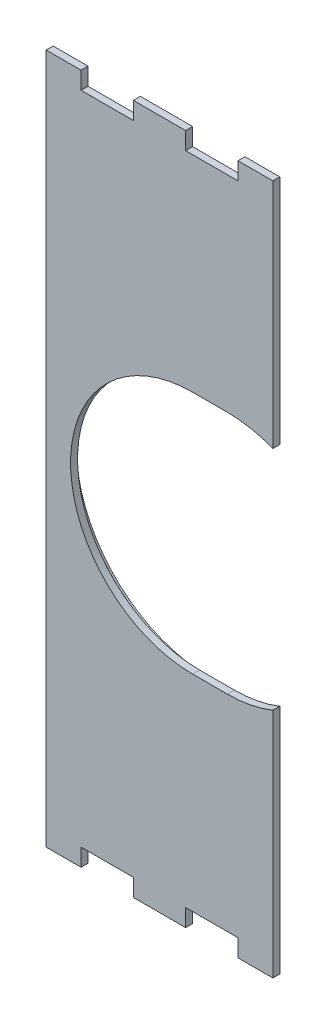
SolidWorks part; units mm, degrees
ref_plane "Front Plane" through (0, 0, 0) normal (0, 0, 1) x (1, 0, 0)
ref_plane "Top Plane" through (0, 0, 0) normal (0, 1, 0) x (1, 0, 0)
ref_plane "Right Plane" through (0, 0, 0) normal (1, 0, 0) x (0, 0, -1)
sketch "Sketch1" plane through (0, 0, 0) normal (0, 0, 1) x (1, 0, 0)
  line L1 (-374.65, -246.38) -> (-292.1, -246.38)
  line L2 (-374.65, -246.38) -> (-374.65, 5.08)
  line L3 (-374.65, 5.08) -> (-292.1, 5.08)
  line L4 (-292.1, -246.38) -> (-292.1, 5.08)
extrude "Boss-Extrude1" add sketch "Sketch1" along normal blind 6.35
sketch "Sketch3" plane through (0, 0, 6.35) normal (0, 0, 1) x (1, 0, 0)
  line L0 (-374.65, -120.65) -> (-351.9735, -120.65) construction
  line L1 (-374.65, 5.08) -> (-374.65, -246.38) construction
sketch "Sketch2" plane through (0, 5.08, 0) normal (0, 1, 0) x (1, 0, 0)
  line L0 (-304.8, 0) -> (-323.85, 0)
  line L1 (-342.9, 0) -> (-361.95, 0)
  line L2 (-374.65, -6.35) -> (-292.1, -6.35)
  line L46 (0, 33.02) -> (-6.35, 33.02)
  line L47 (-6.35, 33.02) -> (-6.35, 50.8)
  line L48 (-6.35, 50.8) -> (0, 50.8)
  line L49 (0, 50.8) -> (0, 69.85)
  line L50 (0, 69.85) -> (-381, 69.85)
  line L51 (-381, 69.85) -> (-381, 57.15)
  line L52 (-381, 57.15) -> (-374.65, 57.15)
  line L53 (-374.65, 57.15) -> (-374.65, 44.45)
  line L54 (-374.65, 44.45) -> (-381, 44.45)
  line L55 (-381, 44.45) -> (-381, 25.4)
  line L56 (-381, 25.4) -> (-374.65, 25.4)
  line L57 (-374.65, 25.4) -> (-374.65, 12.7)
  line L58 (-374.65, 12.7) -> (-381, 12.7)
  line L59 (-381, 12.7) -> (-381, 0)
  line L60 (-374.65, -6.35) -> (-374.65, 0)
  line L61 (-374.65, 0) -> (-361.95, 0)
  line L62 (-361.95, 0) -> (-361.95, -6.35)
  line L63 (-361.95, -6.35) -> (-342.9, -6.35)
  line L64 (-342.9, -6.35) -> (-342.9, 0)
  line L65 (-342.9, 0) -> (-323.85, 0)
  line L66 (-323.85, 0) -> (-323.85, -6.35)
  line L67 (-323.85, -6.35) -> (-304.8, -6.35)
  line L68 (-304.8, -6.35) -> (-304.8, 0)
  line L69 (-304.8, 0) -> (-292.1, 0)
  line L70 (-292.1, 0) -> (-292.1, -6.35)
  line L71 (-292.1, -6.35) -> (-285.75, -6.35)
  line L72 (-285.75, -6.35) -> (-285.75, 44.45)
  line L73 (-279.4, 50.8) -> (-215.9, 50.8)
  line L74 (-209.55, 44.45) -> (-209.55, -57.15)
  line L75 (-215.9, -63.5) -> (-215.9, -69.85)
  line L76 (-215.9, -69.85) -> (-196.85, -69.85)
  line L77 (-196.85, -69.85) -> (-196.85, -63.5)
  line L78 (-203.2, -57.15) -> (-203.2, 44.45)
  line L79 (-196.85, 50.8) -> (-131.8807, 50.8)
  line L80 (-125.7444, 46.0836) -> (-113.8144, 1.27)
  line L81 (-97.0614, 1.27) -> (-6.35, 1.27)
  line L82 (-97.0614, 1.27) -> (-6.35, 1.27)
  line L83 (-113.8144, 1.27) -> (-107.597, 1.27)
  line L84 (-113.8144, 1.27) -> (-107.597, 1.27)
  line L89 (-6.35, 1.27) -> (-6.35, 13.97)
  line L90 (-6.35, 13.97) -> (0, 13.97)
  line L91 (0, 13.97) -> (0, 33.02)
  line L106 (-374.65, -6.35) -> (-374.65, 0)
  line L107 (-374.65, 0) -> (-361.95, 0)
  line L108 (-361.95, 0) -> (-361.95, -6.35)
  line L109 (-361.95, -6.35) -> (-342.9, -6.35)
  line L110 (-342.9, -6.35) -> (-342.9, 0)
  line L111 (-342.9, 0) -> (-323.85, 0)
  line L112 (-323.85, 0) -> (-323.85, -6.35)
  line L113 (-323.85, -6.35) -> (-304.8, -6.35)
  line L114 (-304.8, -6.35) -> (-304.8, 0)
  line L115 (-304.8, 0) -> (-292.1, 0)
  line L116 (-292.1, 0) -> (-292.1, -6.35)
  arc A7 (-381, 0) -> (-374.65, -6.35) centre (-374.65, 0) ccw
  arc A8 (-279.4, 50.8) -> (-285.75, 44.45) centre (-279.4, 44.45) ccw
  arc A9 (-209.55, 44.45) -> (-215.9, 50.8) centre (-215.9, 44.45) ccw
  arc A10 (-215.9, -63.5) -> (-209.55, -57.15) centre (-215.9, -57.15) ccw
  arc A11 (-203.2, -57.15) -> (-196.85, -63.5) centre (-196.85, -57.15) ccw
  arc A12 (-196.85, 50.8) -> (-203.2, 44.45) centre (-196.85, 44.45) ccw
  arc A13 (-125.7444, 46.0836) -> (-131.8807, 50.8) centre (-131.8807, 44.45) ccw
  ellipse E2 centre (-102.3292, 8.5961) end of major axis (-102.3292, -2.0421) minor radius 7.2651 (-97.0614, 1.27) -> (-107.597, 1.27) ccw
  ellipse E3 centre (-102.3292, 8.5961) end of major axis (-102.3292, -2.0421) minor radius 7.2651 (-97.0614, 1.27) -> (-107.597, 1.27) ccw
  line M55 (-292.1, 0) -> (-374.65, 0)
  dimension "D1" = 0
extrude "Cut-Extrude2" cut sketch "Sketch2" against normal blind 6.35 contours L2 L110 L108 M55 | L2 L114 L112 M55
sketch "Sketch5" plane through (0, -246.38, 0) normal (0, -1, 0) x (1, 0, 0)
  line L0 (-374.65, 6.35) -> (-351.9735, 6.35) construction
  line L1 (-361.95, 6.35) -> (-342.9, 6.35)
  line L2 (-361.95, 6.35) -> (-361.95, 0)
  line L3 (-361.95, 0) -> (-342.9, 0)
  line L4 (-342.9, 6.35) -> (-342.9, 0)
  line L5 (-374.65, 0) -> (-292.1, 0) construction
  line L6 (-374.65, 6.35) -> (-292.1, 6.35) construction
  line L7 (-323.85, 6.35) -> (-304.8, 6.35)
  line L8 (-323.85, 6.35) -> (-323.85, 0)
  line L9 (-323.85, 0) -> (-304.8, 0)
  line L10 (-304.8, 6.35) -> (-304.8, 0)
  line L11 (-374.65, 6.35) -> (-374.65, 0) construction
  line L12 (-342.9, 6.35) -> (-342.9, 0) construction
  line M5 (-374.65, 0) -> (-292.1, 0)
  line M7 (-292.1, 6.35) -> (-374.65, 6.35)
  dimension "D1" = 12.7
  dimension "D2" = 19.05
  dimension "D3" = 19.05
  dimension "D4" = 19.05
extrude "Cut-Extrude4" cut sketch "Sketch5" against normal blind 6.35 contours L4 L2 M7 M5 | L10 L8 M7 M5
sketch "Sketch6" plane through (0, 0, 6.35) normal (0, 0, 1) x (1, 0, 0)
  line L0 (-321.31, -165.1) -> (-308.61, -165.1)
  line L1 (-321.31, -76.2) -> (-308.61, -76.2)
  line L2 (-374.65, 5.08) -> (-374.65, -246.38) construction
  arc A0 (-321.31, -76.2) -> (-321.31, -165.1) centre (-321.31, -120.65) ccw
  arc A1 (-308.61, -165.1) -> (-308.61, -76.2) centre (-308.61, -120.65) ccw
  dimension "D1" = 88.9
  dimension "D2" = 88.9
  dimension "D3" = 12.7
  dimension "D4" = 53.34
extrude "Cut-Extrude5" cut sketch "Sketch6" against normal through all
sketch "Sketch8" plane through (0, 0, 0) normal (0, 0, -1) x (-1, 0, 0)
  line L46 (308.61, -74.422) -> (321.31, -74.422)
  line L47 (321.31, -166.878) -> (308.61, -166.878)
  line L48 (293.878, -164.4678) -> (293.878, -244.602)
  line L49 (293.878, -244.602) -> (303.022, -244.602)
  line L50 (303.022, -244.602) -> (303.022, -238.252)
  line L51 (303.022, -238.252) -> (325.628, -238.252)
  line L52 (325.628, -238.252) -> (325.628, -244.602)
  line L53 (325.628, -244.602) -> (341.122, -244.602)
  line L54 (341.122, -244.602) -> (341.122, -238.252)
  line L55 (341.122, -238.252) -> (363.728, -238.252)
  line L56 (363.728, -238.252) -> (363.728, -244.602)
  line L57 (363.728, -244.602) -> (372.872, -244.602)
  line L58 (372.872, -244.602) -> (372.872, 3.302)
  line L59 (372.872, 3.302) -> (363.728, 3.302)
  line L60 (363.728, 3.302) -> (363.728, -3.048)
  line L61 (363.728, -3.048) -> (341.122, -3.048)
  line L62 (341.122, -3.048) -> (341.122, 3.302)
  line L63 (341.122, 3.302) -> (325.628, 3.302)
  line L64 (325.628, 3.302) -> (325.628, -3.048)
  line L65 (325.628, -3.048) -> (303.022, -3.048)
  line L66 (303.022, -3.048) -> (303.022, 3.302)
  line L67 (303.022, 3.302) -> (293.878, 3.302)
  line L68 (293.878, 3.302) -> (293.878, -76.8322)
  line L69 (308.61, -74.422) -> (321.31, -74.422)
  line L70 (321.31, -166.878) -> (308.61, -166.878)
  line L71 (293.878, -164.4678) -> (293.878, -244.602)
  line L72 (293.878, -244.602) -> (303.022, -244.602)
  line L73 (303.022, -244.602) -> (303.022, -238.252)
  line L74 (303.022, -238.252) -> (325.628, -238.252)
  line L75 (325.628, -238.252) -> (325.628, -244.602)
  line L76 (325.628, -244.602) -> (341.122, -244.602)
  line L77 (341.122, -244.602) -> (341.122, -238.252)
  line L78 (341.122, -238.252) -> (363.728, -238.252)
  line L79 (363.728, -238.252) -> (363.728, -244.602)
  line L80 (363.728, -244.602) -> (372.872, -244.602)
  line L81 (372.872, -244.602) -> (372.872, 3.302)
  line L82 (372.872, 3.302) -> (363.728, 3.302)
  line L83 (363.728, 3.302) -> (363.728, -3.048)
  line L84 (363.728, -3.048) -> (341.122, -3.048)
  line L85 (341.122, -3.048) -> (341.122, 3.302)
  line L86 (341.122, 3.302) -> (325.628, 3.302)
  line L87 (325.628, 3.302) -> (325.628, -3.048)
  line L88 (325.628, -3.048) -> (303.022, -3.048)
  line L89 (303.022, -3.048) -> (303.022, 3.302)
  line L90 (303.022, 3.302) -> (293.878, 3.302)
  line L91 (293.878, 3.302) -> (293.878, -76.8322)
  arc A6 (308.61, -74.422) -> (293.878, -76.8322) centre (308.61, -120.65) ccw
  arc A7 (321.31, -166.878) -> (321.31, -74.422) centre (321.31, -120.65) ccw
  arc A8 (293.878, -164.4678) -> (308.61, -166.878) centre (308.61, -120.65) ccw
  arc A9 (308.61, -74.422) -> (293.878, -76.8322) centre (308.61, -120.65) ccw
  arc A10 (321.31, -166.878) -> (321.31, -74.422) centre (321.31, -120.65) ccw
  arc A11 (293.878, -164.4678) -> (308.61, -166.878) centre (308.61, -120.65) ccw
  arc M27 (292.1, -79.3799) -> (308.61, -76.2) centre (308.61, -120.65) cw
  line M28 (308.61, -76.2) -> (321.31, -76.2)
  arc M29 (321.31, -76.2) -> (321.31, -165.1) centre (321.31, -120.65) cw
  line M30 (321.31, -165.1) -> (308.61, -165.1)
  arc M31 (308.61, -165.1) -> (292.1, -161.9201) centre (308.61, -120.65) cw
  line M32 (292.1, -161.9201) -> (292.1, -246.38)
  line M33 (292.1, -246.38) -> (304.8, -246.38)
  line M34 (304.8, -246.38) -> (304.8, -240.03)
  line M35 (304.8, -240.03) -> (323.85, -240.03)
  line M36 (323.85, -240.03) -> (323.85, -246.38)
  line M37 (323.85, -246.38) -> (342.9, -246.38)
  line M38 (342.9, -246.38) -> (342.9, -240.03)
  line M39 (342.9, -240.03) -> (361.95, -240.03)
  line M40 (361.95, -240.03) -> (361.95, -246.38)
  line M41 (361.95, -246.38) -> (374.65, -246.38)
  line M42 (374.65, -246.38) -> (374.65, 5.08)
  line M43 (374.65, 5.08) -> (361.95, 5.08)
  line M44 (361.95, 5.08) -> (361.95, -1.27)
  line M45 (361.95, -1.27) -> (342.9, -1.27)
  line M46 (342.9, -1.27) -> (342.9, 5.08)
  line M47 (342.9, 5.08) -> (323.85, 5.08)
  line M48 (323.85, 5.08) -> (323.85, -1.27)
  line M49 (323.85, -1.27) -> (304.8, -1.27)
  line M50 (304.8, -1.27) -> (304.8, 5.08)
  line M51 (304.8, 5.08) -> (292.1, 5.08)
  line M52 (292.1, 5.08) -> (292.1, -79.3799)
  dimension "D1" = 1.778
extrude "Cut-Extrude6" cut sketch "Sketch8" against normal blind 3.81 contours L71 A11 L70 A10 L69 A9 L91 L90 L89 L88 L87 L86 L85 L84 L83 L82 L81 L80 L79 L78 L77 L76 L75 L74 M52 M27 M28 M29 M30 M31 M32 M33 M34 M35 M36 M37 M38 M39 M40 M41 M42 M43 M44 M45 M46 M47 M48 M49 M50 M51
sketch "Sketch9" plane through (0, 0, 0) normal (0, 0, -1) x (-1, 0, 0)
  line L46 (295.656, -166.8752) -> (295.656, -242.824)
  line L47 (295.656, -242.824) -> (301.244, -242.824)
  line L48 (301.244, -242.824) -> (301.244, -236.474)
  line L49 (301.244, -236.474) -> (327.406, -236.474)
  line L50 (327.406, -236.474) -> (327.406, -242.824)
  line L51 (327.406, -242.824) -> (339.344, -242.824)
  line L52 (339.344, -242.824) -> (339.344, -236.474)
  line L53 (339.344, -236.474) -> (365.506, -236.474)
  line L54 (365.506, -236.474) -> (365.506, -242.824)
  line L55 (365.506, -242.824) -> (371.094, -242.824)
  line L56 (371.094, -242.824) -> (371.094, 1.524)
  line L57 (371.094, 1.524) -> (365.506, 1.524)
  line L58 (365.506, 1.524) -> (365.506, -4.826)
  line L59 (365.506, -4.826) -> (339.344, -4.826)
  line L60 (339.344, -4.826) -> (339.344, 1.524)
  line L61 (339.344, 1.524) -> (327.406, 1.524)
  line L62 (327.406, 1.524) -> (327.406, -4.826)
  line L63 (327.406, -4.826) -> (301.244, -4.826)
  line L64 (301.244, -4.826) -> (301.244, 1.524)
  line L65 (301.244, 1.524) -> (295.656, 1.524)
  line L66 (295.656, 1.524) -> (295.656, -74.4248)
  line L67 (308.61, -72.644) -> (321.31, -72.644)
  line L68 (321.31, -168.656) -> (308.61, -168.656)
  line L69 (295.656, -166.8752) -> (295.656, -242.824)
  line L70 (295.656, -242.824) -> (301.244, -242.824)
  line L71 (301.244, -242.824) -> (301.244, -236.474)
  line L72 (301.244, -236.474) -> (327.406, -236.474)
  line L73 (327.406, -236.474) -> (327.406, -242.824)
  line L74 (327.406, -242.824) -> (339.344, -242.824)
  line L75 (339.344, -242.824) -> (339.344, -236.474)
  line L76 (339.344, -236.474) -> (365.506, -236.474)
  line L77 (365.506, -236.474) -> (365.506, -242.824)
  line L78 (365.506, -242.824) -> (371.094, -242.824)
  line L79 (371.094, -242.824) -> (371.094, 1.524)
  line L80 (371.094, 1.524) -> (365.506, 1.524)
  line L81 (365.506, 1.524) -> (365.506, -4.826)
  line L82 (365.506, -4.826) -> (339.344, -4.826)
  line L83 (339.344, -4.826) -> (339.344, 1.524)
  line L84 (339.344, 1.524) -> (327.406, 1.524)
  line L85 (327.406, 1.524) -> (327.406, -4.826)
  line L86 (327.406, -4.826) -> (301.244, -4.826)
  line L87 (301.244, -4.826) -> (301.244, 1.524)
  line L88 (301.244, 1.524) -> (295.656, 1.524)
  line L89 (295.656, 1.524) -> (295.656, -74.4248)
  line L90 (308.61, -72.644) -> (321.31, -72.644)
  line L91 (321.31, -168.656) -> (308.61, -168.656)
  arc A6 (295.656, -166.8752) -> (308.61, -168.656) centre (308.61, -120.65) ccw
  arc A7 (308.61, -72.644) -> (295.656, -74.4248) centre (308.61, -120.65) ccw
  arc A8 (321.31, -168.656) -> (321.31, -72.644) centre (321.31, -120.65) ccw
  arc A9 (295.656, -166.8752) -> (308.61, -168.656) centre (308.61, -120.65) ccw
  arc A10 (308.61, -72.644) -> (295.656, -74.4248) centre (308.61, -120.65) ccw
  arc A11 (321.31, -168.656) -> (321.31, -72.644) centre (321.31, -120.65) ccw
  arc M27 (308.61, -166.878) -> (293.878, -164.4678) centre (308.61, -120.65) cw
  line M28 (293.878, -164.4678) -> (293.878, -244.602)
  line M29 (293.878, -244.602) -> (303.022, -244.602)
  line M30 (303.022, -244.602) -> (303.022, -238.252)
  line M31 (303.022, -238.252) -> (325.628, -238.252)
  line M32 (325.628, -238.252) -> (325.628, -244.602)
  line M33 (325.628, -244.602) -> (341.122, -244.602)
  line M34 (341.122, -244.602) -> (341.122, -238.252)
  line M35 (341.122, -238.252) -> (363.728, -238.252)
  line M36 (363.728, -238.252) -> (363.728, -244.602)
  line M37 (363.728, -244.602) -> (372.872, -244.602)
  line M38 (372.872, -244.602) -> (372.872, 3.302)
  line M39 (372.872, 3.302) -> (363.728, 3.302)
  line M40 (363.728, 3.302) -> (363.728, -3.048)
  line M41 (363.728, -3.048) -> (341.122, -3.048)
  line M42 (341.122, -3.048) -> (341.122, 3.302)
  line M43 (341.122, 3.302) -> (325.628, 3.302)
  line M44 (325.628, 3.302) -> (325.628, -3.048)
  line M45 (325.628, -3.048) -> (303.022, -3.048)
  line M46 (303.022, -3.048) -> (303.022, 3.302)
  line M47 (303.022, 3.302) -> (293.878, 3.302)
  line M48 (293.878, 3.302) -> (293.878, -76.8322)
  arc M49 (293.878, -76.8322) -> (308.61, -74.422) centre (308.61, -120.65) cw
  line M50 (308.61, -74.422) -> (321.31, -74.422)
  arc M51 (321.31, -74.422) -> (321.31, -166.878) centre (321.31, -120.65) cw
  line M52 (321.31, -166.878) -> (308.61, -166.878)
  dimension "D1" = 1.778
extrude "Cut-Extrude7" cut sketch "Sketch9" against normal blind 2.54 contours L91 A11 L90 A10 L89 L88 L87 L86 L85 L84 L83 L82 L81 L80 L79 L78 L77 L76 L75 L74 L73 L72 L71 L70 M52 M27 M28 M29 M30 M31 M32 M33 M34 M35 M36 M37 M38 M39 M40 M41 M42 M43 M44 M45 M46 M47 M48 M49 M50 M51
sketch "Sketch10" plane through (0, 0, 0) normal (0, 0, -1) x (-1, 0, 0)
  line L46 (321.31, -169.418) -> (308.61, -169.418)
  line L47 (296.418, -167.8694) -> (296.418, -242.062)
  line L48 (296.418, -242.062) -> (300.482, -242.062)
  line L49 (300.482, -242.062) -> (300.482, -235.712)
  line L50 (300.482, -235.712) -> (328.168, -235.712)
  line L51 (328.168, -235.712) -> (328.168, -242.062)
  line L52 (328.168, -242.062) -> (338.582, -242.062)
  line L53 (338.582, -242.062) -> (338.582, -235.712)
  line L54 (338.582, -235.712) -> (366.268, -235.712)
  line L55 (366.268, -235.712) -> (366.268, -242.062)
  line L56 (366.268, -242.062) -> (370.332, -242.062)
  line L57 (370.332, -242.062) -> (370.332, 0.762)
  line L58 (370.332, 0.762) -> (366.268, 0.762)
  line L59 (370.332, 0.762) -> (366.268, 0.762)
  line L60 (366.268, 0.762) -> (366.268, -5.588)
  line L61 (366.268, 0.762) -> (366.268, -5.588)
  line L62 (366.268, -5.588) -> (338.582, -5.588)
  line L63 (366.268, -5.588) -> (338.582, -5.588)
  line L64 (338.582, -5.588) -> (338.582, 0.762)
  line L65 (338.582, -5.588) -> (338.582, 0.762)
  line L66 (338.582, 0.762) -> (328.168, 0.762)
  line L67 (338.582, 0.762) -> (328.168, 0.762)
  line L68 (328.168, 0.762) -> (328.168, -5.588)
  line L69 (321.31, -169.418) -> (308.61, -169.418)
  line L70 (296.418, -167.8694) -> (296.418, -242.062)
  line L71 (296.418, -242.062) -> (300.482, -242.062)
  line L72 (300.482, -242.062) -> (300.482, -235.712)
  line L73 (300.482, -235.712) -> (328.168, -235.712)
  line L74 (328.168, -235.712) -> (328.168, -242.062)
  line L75 (328.168, -242.062) -> (338.582, -242.062)
  line L76 (338.582, -242.062) -> (338.582, -235.712)
  line L77 (338.582, -235.712) -> (366.268, -235.712)
  line L78 (366.268, -235.712) -> (366.268, -242.062)
  line L79 (366.268, -242.062) -> (370.332, -242.062)
  line L80 (370.332, -242.062) -> (370.332, 0.762)
  line L92 (328.168, 0.762) -> (328.168, -5.588)
  line L93 (328.168, -5.588) -> (300.482, -5.588)
  line L94 (328.168, -5.588) -> (300.482, -5.588)
  line L95 (300.482, -5.588) -> (300.482, 0.762)
  line L96 (300.482, -5.588) -> (300.482, 0.762)
  line L97 (300.482, 0.762) -> (296.418, 0.762)
  line L98 (300.482, 0.762) -> (296.418, 0.762)
  line L99 (296.418, 0.762) -> (296.418, -73.4306)
  line L100 (296.418, 0.762) -> (296.418, -73.4306)
  line L101 (308.61, -71.882) -> (321.31, -71.882)
  line L102 (308.61, -71.882) -> (321.31, -71.882)
  arc A6 (321.31, -169.418) -> (321.31, -71.882) centre (321.31, -120.65) ccw
  arc A7 (296.418, -167.8694) -> (308.61, -169.418) centre (308.61, -120.65) ccw
  arc A8 (308.61, -71.882) -> (296.418, -73.4306) centre (308.61, -120.65) ccw
  arc A9 (321.31, -169.418) -> (321.31, -71.882) centre (321.31, -120.65) ccw
  arc A10 (296.418, -167.8694) -> (308.61, -169.418) centre (308.61, -120.65) ccw
  arc A12 (308.61, -71.882) -> (296.418, -73.4306) centre (308.61, -120.65) ccw
  arc M27 (321.31, -72.644) -> (321.31, -168.656) centre (321.31, -120.65) cw
  line M28 (321.31, -168.656) -> (308.61, -168.656)
  arc M29 (308.61, -168.656) -> (295.656, -166.8752) centre (308.61, -120.65) cw
  line M30 (295.656, -166.8752) -> (295.656, -242.824)
  line M31 (295.656, -242.824) -> (301.244, -242.824)
  line M32 (301.244, -242.824) -> (301.244, -236.474)
  line M33 (301.244, -236.474) -> (327.406, -236.474)
  line M34 (327.406, -236.474) -> (327.406, -242.824)
  line M35 (327.406, -242.824) -> (339.344, -242.824)
  line M36 (339.344, -242.824) -> (339.344, -236.474)
  line M37 (339.344, -236.474) -> (365.506, -236.474)
  line M38 (365.506, -236.474) -> (365.506, -242.824)
  line M39 (365.506, -242.824) -> (371.094, -242.824)
  line M40 (371.094, -242.824) -> (371.094, 1.524)
  line M41 (371.094, 1.524) -> (365.506, 1.524)
  line M42 (365.506, 1.524) -> (365.506, -4.826)
  line M43 (365.506, -4.826) -> (339.344, -4.826)
  line M44 (339.344, -4.826) -> (339.344, 1.524)
  line M45 (339.344, 1.524) -> (327.406, 1.524)
  line M46 (327.406, 1.524) -> (327.406, -4.826)
  line M47 (327.406, -4.826) -> (301.244, -4.826)
  line M48 (301.244, -4.826) -> (301.244, 1.524)
  line M49 (301.244, 1.524) -> (295.656, 1.524)
  line M50 (295.656, 1.524) -> (295.656, -74.4248)
  arc M51 (295.656, -74.4248) -> (308.61, -72.644) centre (308.61, -120.65) cw
  line M52 (308.61, -72.644) -> (321.31, -72.644)
  dimension "D1" = 0.762
extrude "Cut-Extrude8" cut sketch "Sketch10" against normal blind 1.27 contours L102 A12 L100 L98 L96 L94 L92 L67 L65 L63 L61 L59 L80 L79 L78 L77 L76 L75 L74 L73 L72 L71 L70 A10 M52 M27 M28 M29 M30 M31 M32 M33 M34 M35 M36 M37 M38 M39 M40 M41 M42 M43 M44 M45 M46 M47 M48 M49 M50 M51
